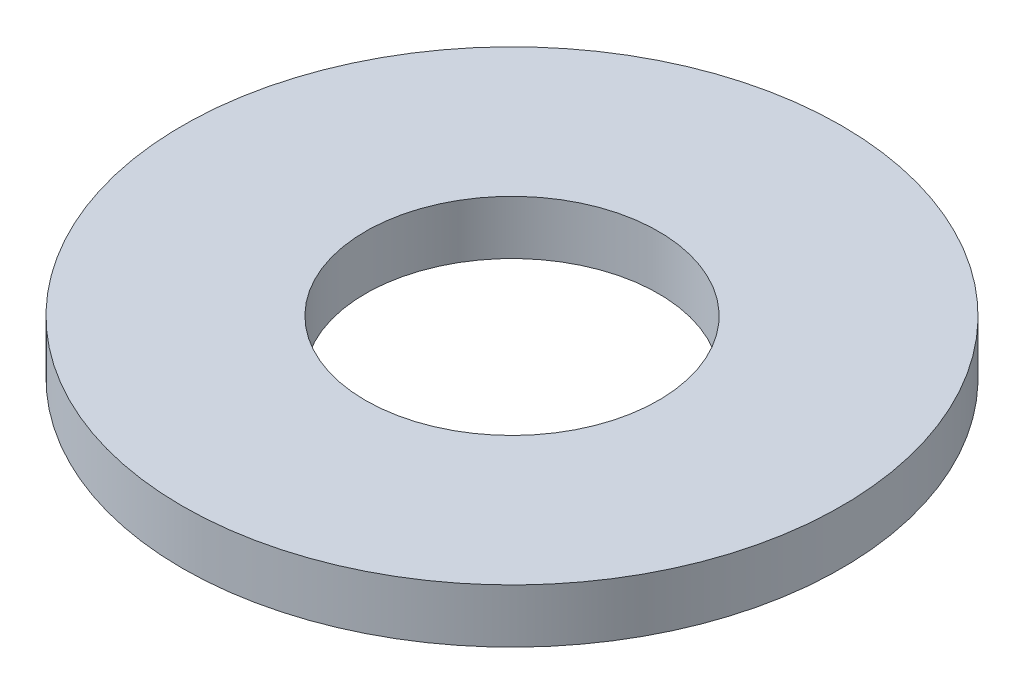
SolidWorks part; units mm, degrees
material "Markforged"
ref_plane "Front Plane" through (0, 0, 0) normal (0, 0, 1) x (1, 0, 0)
ref_plane "Top Plane" through (0, 0, 0) normal (0, 1, 0) x (1, 0, 0)
ref_plane "Right Plane" through (0, 0, 0) normal (1, 0, 0) x (0, 0, -1)
other "Bounding Box"
ref_plane "Default Plane" through (13.8565, 3.175, 6.7999) normal (0, -1, 0) x (-1, 0, 0)
sketch "Sketch1" plane through (0, 0, 0) normal (0, 1, 0) x (1, 0, 0)
  circle A0 centre (0, 0) radius 6.35
  circle A1 centre (0, 0) radius 14.2875
  dimension "D1" = 12.7
  dimension "D2" = 28.575
extrude "Boss-Extrude1" add sketch "Sketch1" along normal blind 2.3368
